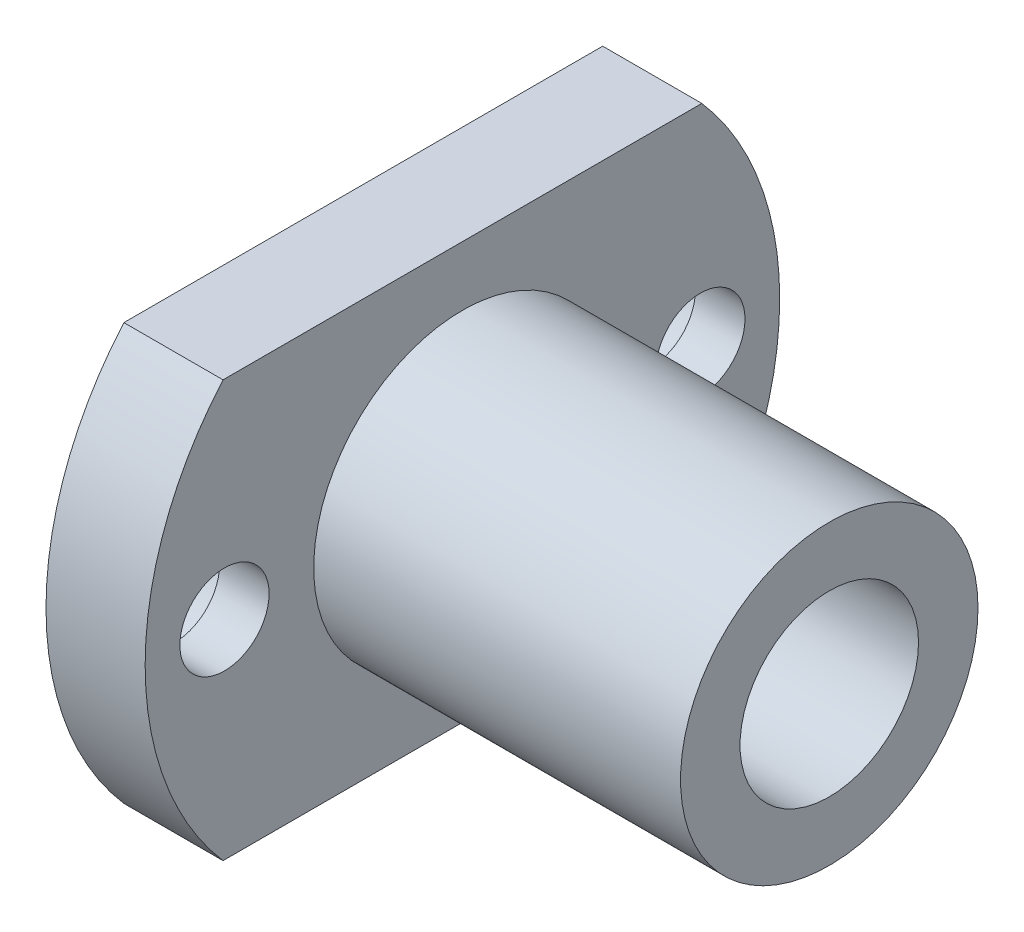
SolidWorks part; units mm, degrees
ref_plane "前视基准面" through (0, 0, 0) normal (0, 0, 1) x (1, 0, 0)
ref_plane "上视基准面" through (0, 0, 0) normal (0, 1, 0) x (1, 0, 0)
ref_plane "右视基准面" through (0, 0, 0) normal (1, 0, 0) x (0, 0, -1)
other "Configuration Table"
sketch "草图1" plane through (0, 0, 0) normal (1, 0, 0) x (0, 0, -1)
  line L0 (0, 0) -> (0, 10.5) construction
  line L1 (-12.0727, 10.5) -> (12.0727, 10.5)
  line L3 (-12.0727, -10.5) -> (12.0727, -10.5)
  arc A0 (-12.0727, 10.5) -> (-12.0727, -10.5) centre (0, 0) ccw
  arc A1 (12.0727, -10.5) -> (12.0727, 10.5) centre (0, 0) ccw
  point P7 (0, 10.5)
  dimension "D1" = 32
  dimension "D2" = 10.5
extrude "凸台-拉伸3" add sketch "草图1" along normal blind 5
sketch "草图3" plane through (5, 0, 0) normal (1, 0, 0) x (0, 0, -1)
  line L0 (-16, 0) -> (16, 0) construction
  circle A0 centre (0, 0) radius 7.5
  arc A1 (12.0727, -10.5) -> (12.0727, 10.5) centre (0, 0) ccw construction
  circle A2 centre (-12, 0) radius 2.25
  circle A3 centre (12, 0) radius 2.25
  circle A4 centre (0, 0) radius 4.5
  point P9 (0, 0)
  dimension "D1" = 15
  dimension "D2" = 4.5
  dimension "D3" = 4.5
  dimension "D4" = 9
  dimension "D5" = 4
  dimension "D6" = 4
extrude "切除-拉伸4" cut sketch "草图3" against normal blind 2.5 contours A2 | A3
sketch "草图5" plane through (5, 0, 0) normal (1, 0, 0) x (0, 0, -1)
  circle A0 centre (0, 0) radius 7.5
  dimension "D1" = 15
extrude "凸台-拉伸4" add sketch "草图5" along normal blind 18.5
sketch "草图6" plane through (23.5, 0, 0) normal (1, 0, 0) x (0, 0, -1)
  circle A0 centre (0, 0) radius 4.5
  dimension "D1" = 9
extrude "切除-拉伸5" cut sketch "草图6" against normal through all
sketch "草图7" plane through (0, 0, 0) normal (-1, 0, 0) x (0, 0, 1)
  line L0 (-16, 0) -> (16, 0) construction
  arc A0 (12.0727, -10.5) -> (12.0727, 10.5) centre (0, 0) ccw construction
  circle A1 centre (-12, 0) radius 3.25
  circle A2 centre (12, 0) radius 3.25
  point P7 (0, 0)
  dimension "D1" = 6.5
  dimension "D2" = 6.5
  dimension "D3" = 12
  dimension "D4" = 12
extrude "切除-拉伸6" cut sketch "草图7" against normal blind 2.5
